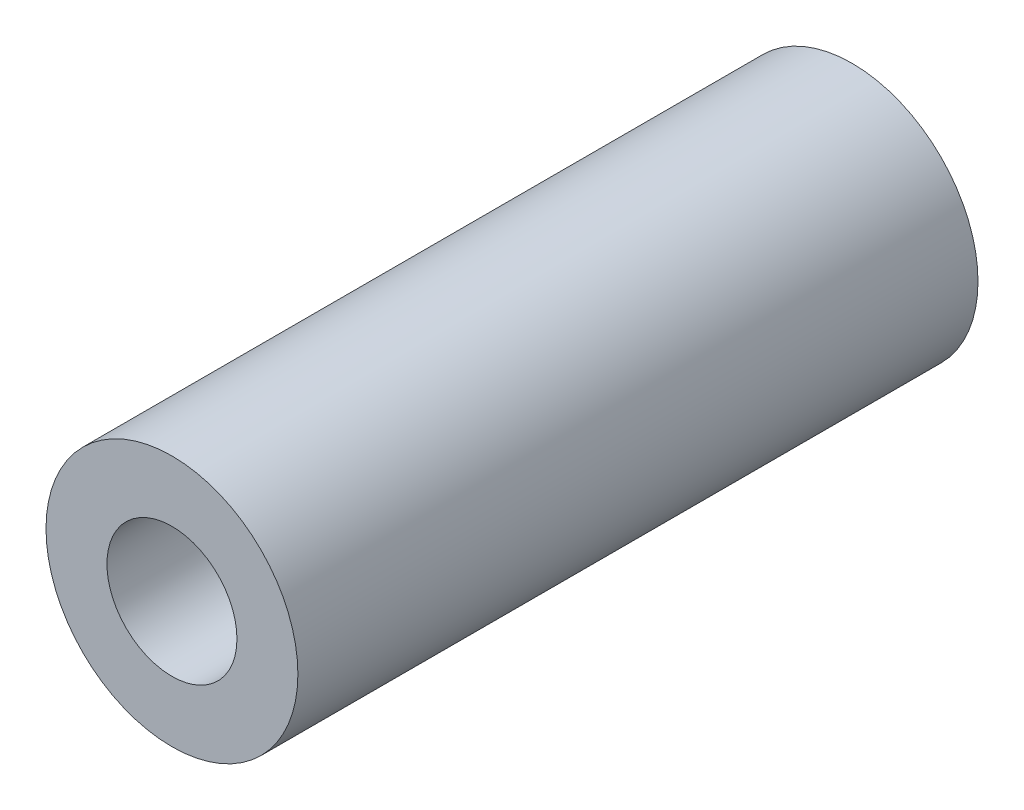
SolidWorks part; units mm, degrees
material "ABS"
ref_plane "Plano frontal" through (0, 0, 0) normal (0, 0, 1) x (1, 0, 0)
ref_plane "Plano superior" through (0, 0, 0) normal (0, 1, 0) x (1, 0, 0)
ref_plane "Plano direito" through (0, 0, 0) normal (1, 0, 0) x (0, 0, -1)
sketch "Esboço1" plane through (0, 0, 0) normal (0, 0, 1) x (1, 0, 0)
  circle A0 centre (16.0167, 16.0167) radius 3.1
  circle A1 centre (16.0167, 16.0167) radius 1.55
  dimension "D1" = 3.1
extrude "Ressalto-extrusão1" add sketch "Esboço1" along normal up to vertex (16.74 mm away)
hole_wizard "M3 Clearance Hole1" positions "3DSketch1" profile "Sketch1" hole size "M3" standard "ISO" end condition through all
sketch3d "3DSketch1"
  line L0 (16.0167, 16.0167, 16.74) -> (16.0167, 16.0167, 0) construction
  line L1 (16.0167, 16.0167, 16.74) -> (16.0167, 16.0167, 0) construction
  point P0 (16.0167, 16.0167, 16.74)
sketch "Sketch1" plane through (16.0167, 16.0167, 16.74) normal (1, 0, 0) x (0, -1, 0)
  line L0 (0, 0) -> (0, 16.74)
  line L1 (0, 16.74) -> (1.6, 16.74)
  line L2 (1.6, 16.74) -> (1.6, 0)
  line L5 (1.6, 0) -> (0, 0)
  line L11 (0, -6.35) -> (0, 107.95) construction
  dimension "Thru Hole Dia." = 3.2
  dimension "Thru Hole Depth" = 16.74
